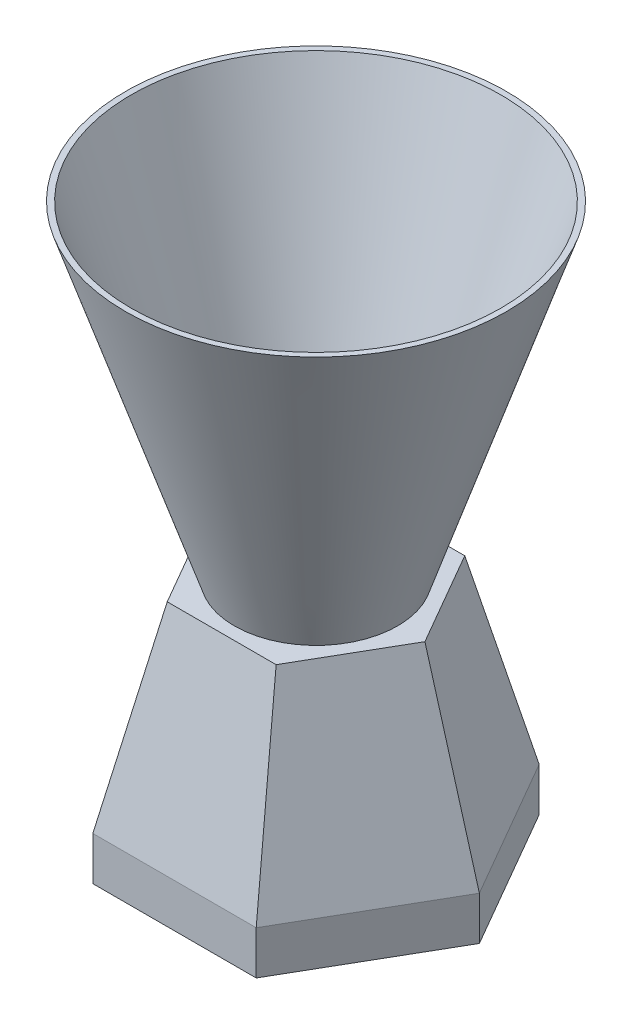
SolidWorks part; units mm, degrees
ref_plane "Front Plane" through (0, 0, 0) normal (0, 0, 1) x (1, 0, 0)
ref_plane "Top Plane" through (0, 0, 0) normal (0, 1, 0) x (1, 0, 0)
ref_plane "Right Plane" through (0, 0, 0) normal (1, 0, 0) x (0, 0, -1)
sketch "Sketch1" plane through (0, 0, 0) normal (0, 1, 0) x (1, 0, 0)
  line L1 (30, 0) -> (15, 25.9808)
  line L2 (15, 25.9808) -> (-15, 25.9808)
  line L3 (-15, 25.9808) -> (-30, 0)
  line L4 (-30, 0) -> (-15, -25.9808)
  line L5 (-15, -25.9808) -> (15, -25.9808)
  line L6 (15, -25.9808) -> (30, 0)
  circle A0 centre (0, 0) radius 25.9808 construction
  dimension "D1" = 30
extrude "Extrude1" add sketch "Sketch1" along normal blind 8
sketch "Sketch2" plane through (0, 8, 0) normal (0, 1, 0) x (1, 0, 0)
  line L1 (30, 0) -> (15, 25.9808)
  line L2 (15, 25.9808) -> (-15, 25.9808)
  line L3 (-15, 25.9808) -> (-30, 0)
  line L4 (-30, 0) -> (-15, -25.9808)
  line L5 (-15, -25.9808) -> (15, -25.9808)
  line L6 (15, -25.9808) -> (30, 0)
  circle A0 centre (0, 0) radius 25.9808 construction
ref_plane "Plane1" through (0, 43, 0) normal (0, 1, 0) x (-1, 0, 0)
sketch "Sketch3" plane through (0, 43, 0) normal (0, 1, 0) x (-1, 0, 0)
  line L1 (20, 0) -> (10, 17.3205)
  line L2 (10, 17.3205) -> (-10, 17.3205)
  line L3 (-10, 17.3205) -> (-20, 0)
  line L4 (-20, 0) -> (-10, -17.3205)
  line L5 (-10, -17.3205) -> (10, -17.3205)
  line L6 (10, -17.3205) -> (20, 0)
  circle A0 centre (0, 0) radius 17.3205 construction
  dimension "D1" = 20
loft "Loft1" add profiles "Sketch2", "Sketch3"
sketch "Sketch4" plane through (0, 0, 0) normal (0, 0, 1) x (1, 0, 0)
  line L0 (0, 43) -> (0, 103) construction
  line L1 (-10, 43) -> (10, 43) construction
  line L2 (0, 103) -> (33.9459, 103) construction
  line L3 (35, 103) -> (15, 43)
  line L4 (10, 43) -> (20, 43) construction
  line L5 (33.9459, 103) -> (13.9459, 43)
  line L6 (34.0513, 103.3162) -> (14.0513, 43.3162) construction
  line L7 (15, 43) -> (13.9459, 43)
  line L8 (33.9459, 103) -> (35, 103)
  dimension "D1" = 60
  dimension "D2" = 35
  dimension "D3" = 15
  dimension "D4" = 1
revolve "Revolve1" add sketch "Sketch4" angle 360 about L0
